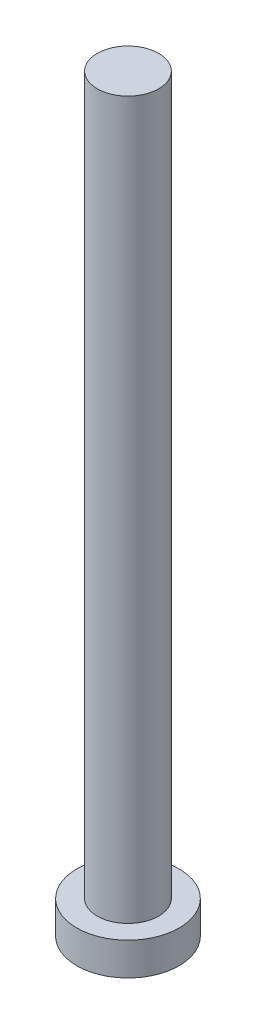
SolidWorks part; units mm, degrees
ref_plane "前视基准面" through (0, 0, 0) normal (0, 0, 1) x (1, 0, 0)
ref_plane "上视基准面" through (0, 0, 0) normal (0, 1, 0) x (1, 0, 0)
ref_plane "右视基准面" through (0, 0, 0) normal (1, 0, 0) x (0, 0, -1)
sketch "草图1" plane through (0, 0, 0) normal (0, 1, 0) x (1, 0, 0)
  circle A0 centre (0, 0) radius 2.5
extrude "凸台-拉伸1" add sketch "草图1" along normal blind 1.6
sketch "草图2" plane through (0, 1.6, 0) normal (0, 1, 0) x (1, 0, 0)
  circle A0 centre (0, 0) radius 1.5
extrude "凸台-拉伸2" add sketch "草图2" along normal blind 35
sketch "草图3" plane through (0, 0, 0) normal (0, -1, 0) x (1, 0, 0)
  line L0 (-0.5, 1) -> (-0.5, 1.75)
  line L1 (-1.75, -0.5) -> (-1, -0.5)
  line L2 (-1.75, -0.5) -> (-1.75, 0.5)
  line L3 (-1.75, 0.5) -> (-1, 0.5)
  line L4 (1.75, -0.5) -> (1.75, 0.5)
  line L5 (-1.75, -0.5) -> (1.75, 0.5) construction
  line L6 (-1.75, 0.5) -> (1.75, -0.5) construction
  line L7 (-0.5, -1.75) -> (0.5, -1.75)
  line L8 (-0.5, -1.75) -> (-0.5, -1)
  line L9 (-0.5, 1.75) -> (0.5, 1.75)
  line L10 (0.5, -1.75) -> (0.5, -1)
  line L11 (-0.5, -1.75) -> (0.5, 1.75) construction
  line L12 (-0.5, 1.75) -> (0.5, -1.75) construction
  line L13 (1, -0.5) -> (1.75, -0.5)
  line L14 (0.5, 1) -> (0.5, 1.75)
  line L15 (1, 0.5) -> (1.75, 0.5)
  arc A0 (1, -0.5) -> (0.5, -1) centre (1, -1) ccw
  arc A1 (-0.5, -1) -> (-1, -0.5) centre (-1, -1) ccw
  arc A2 (0.5, 1) -> (1, 0.5) centre (1, 1) ccw
  arc A3 (-0.5, 1) -> (-1, 0.5) centre (-1, 1) cw
  point P0 (0, 0)
  point P6 (0, 0)
  point P21 (0.5, 0.5)
  dimension "D1" = 0.5
extrude "切除-拉伸1" cut sketch "草图3" against normal blind 1
